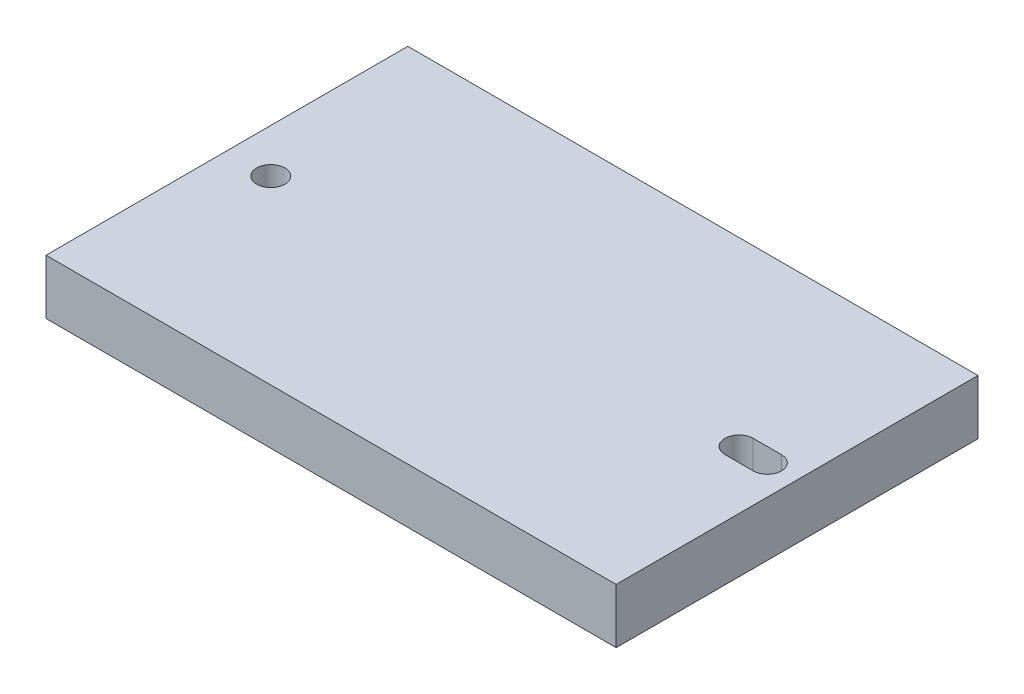
SolidWorks part; units mm, degrees
ref_plane "Front Plane" through (0, 0, 0) normal (0, 0, 1) x (1, 0, 0)
ref_plane "Top Plane" through (0, 0, 0) normal (0, 1, 0) x (1, 0, 0)
ref_plane "Right Plane" through (0, 0, 0) normal (1, 0, 0) x (0, 0, -1)
sketch "Sketch1" plane through (0, 0, 0) normal (0, 1, 0) x (1, 0, 0)
  line L1 (-42.7686, 22.2552) -> (23.2714, 22.2552)
  line L2 (-42.7686, 22.2552) -> (-42.7686, -19.6548)
  line L3 (-42.7686, -19.6548) -> (23.2714, -19.6548)
  line L4 (23.2714, 22.2552) -> (23.2714, -19.6548)
  dimension "D1" = 66.04
  dimension "D2" = 41.91
extrude "Boss-Extrude1" add sketch "Sketch1" along normal blind 6.35
hole_wizard "#5 Clearance Hole1" positions "Sketch12" profile "Sketch11" hole size "#5" standard "Ansi Inch"
sketch "Sketch12" plane through (0, 6.35, 0) normal (0, 1, 0) x (-1, 0, 0)
  line L0 (42.7686, -22.2552) -> (42.7686, 19.6548) construction
  line L1 (-23.2714, -22.2552) -> (42.7686, -22.2552) construction
  point P0 (37.6886, -1.3002)
  dimension "D1" = 5.08
  dimension "D2" = 20.955
sketch "Sketch11" plane through (-37.6886, 6.35, -1.3002) normal (1, 0, 0) x (0, 0, 1)
  line L0 (0, 0) -> (0, 13.6806)
  line L1 (0, 13.6806) -> (1.6319, 12.7)
  line L2 (1.6319, 12.7) -> (1.6319, 0)
  line L5 (1.6319, 0) -> (0, 0)
  line L10 (0, 13.6806) -> (-1.632, 12.7) construction
  line L11 (0, -6.35) -> (0, 107.95) construction
  dimension "Hole Dia." = 3.2639
  dimension "Hole Depth" = 12.7
  dimension "Drill Angle" = 118
sketch "Sketch13" plane through (0, 6.35, 0) normal (0, 1, 0) x (1, 0, 0)
  line L0 (19.8297, 1.3002) -> (16.5531, 1.3002) construction
  line L1 (19.8297, -0.3318) -> (16.5531, -0.3318)
  line L2 (19.8297, 2.9321) -> (16.5531, 2.9321)
  arc A0 (19.8297, -0.3318) -> (19.8297, 2.9321) centre (19.8297, 1.3002) ccw
  arc A1 (16.5531, 2.9321) -> (16.5531, -0.3318) centre (16.5531, 1.3002) ccw
  circle A2 centre (-37.6886, 1.3002) radius 1.632 construction
  point P3 (18.1914, 1.3002)
  dimension "D1" = 55.88
  dimension "D2" = 3.2766
  dimension "D3" = 3.2639
extrude "Cut-Extrude1" cut sketch "Sketch13" against normal up to next
equation "\"D2@Sketch12\" = \"D2@Sketch1\"/2"
